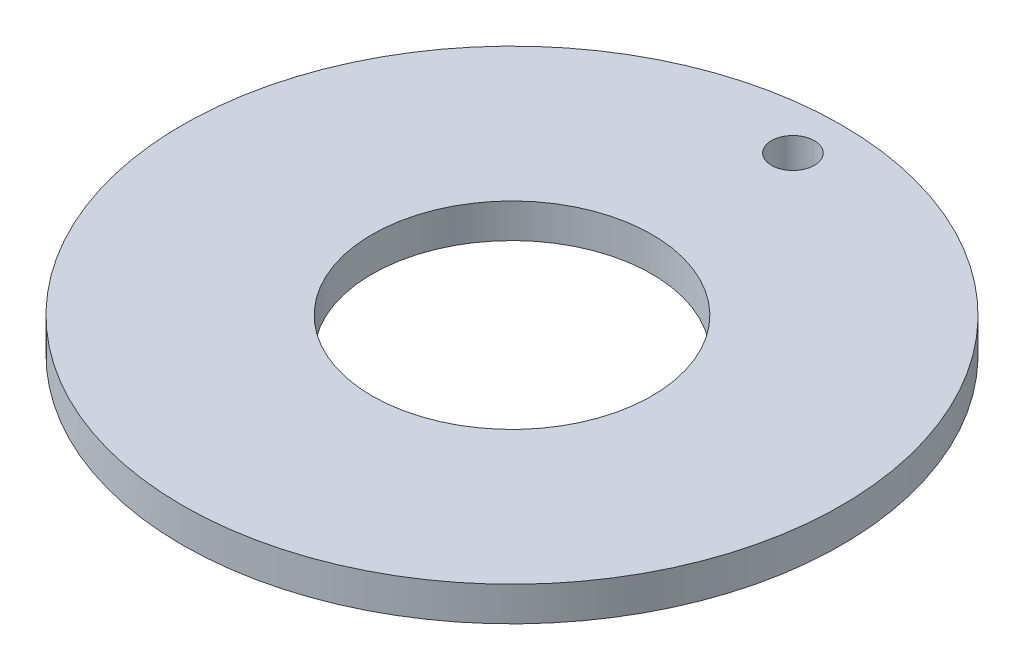
SolidWorks part; units mm, degrees
material "6061-T6 (SS)"
ref_plane "Front Plane" through (0, 0, 0) normal (0, 0, 1) x (1, 0, 0)
ref_plane "Top Plane" through (0, 0, 0) normal (0, 1, 0) x (1, 0, 0)
ref_plane "Right Plane" through (0, 0, 0) normal (1, 0, 0) x (0, 0, -1)
sketch "Sketch1" plane through (0, 0, 0) normal (0, 1, 0) x (1, 0, 0)
  circle A0 centre (0, 0) radius 25.9
  circle A1 centre (0, 0) radius 61
  dimension "D1" = 122
  dimension "D2" = 51.8
extrude "Boss-Extrude1" add sketch "Sketch1" along normal blind 6.35
hole_wizard "5/16 (0.3125) Diameter Hole1" positions "Sketch3" profile "Sketch4" hole size "5/16" standard "ANSI Inch" end condition through all
sketch "Sketch3" plane through (0, 6.35, 0) normal (0, 1, 0) x (1, 0, 0)
  line L0 (0, 52) -> (0, 0) construction
  point P0 (0, 52)
  dimension "D1" = 52
sketch "Sketch4" plane through (0, 6.35, -52) normal (1, 0, 0) x (0, 0, 1)
  line L0 (0, 0) -> (0, 6.35)
  line L1 (0, 6.35) -> (3.9687, 6.35)
  line L2 (3.9687, 6.35) -> (3.9687, 0)
  line L5 (3.9687, 0) -> (0, 0)
  line L11 (0, -6.35) -> (0, 107.95) construction
  dimension "Thru Hole Dia." = 7.9375
  dimension "Thru Hole Depth" = 6.35
